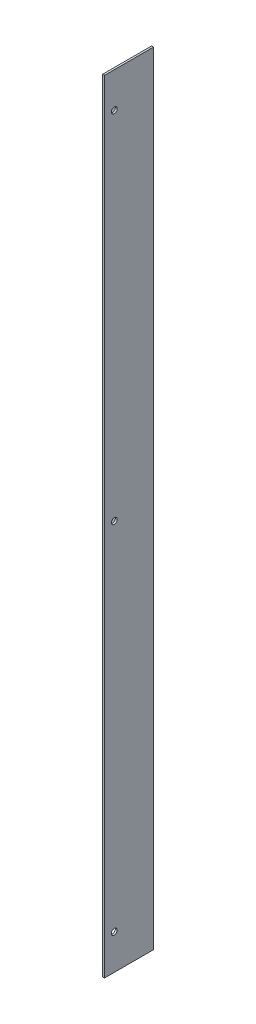
SolidWorks part; units mm, degrees
material "Plástico personalizado"
ref_plane "Alzado" through (0, 0, 0) normal (0, 0, 1) x (1, 0, 0)
ref_plane "Planta" through (0, 0, 0) normal (0, 1, 0) x (1, 0, 0)
ref_plane "Vista lateral" through (0, 0, 0) normal (1, 0, 0) x (0, 0, -1)
sketch "Croquis1" plane through (0, 0, 0) normal (0, 0, 1) x (1, 0, 0)
  line L0 (-79.4418, 83.1804) -> (-79.4418, -268.8196)
  line L2 (-55.4418, 107.1804) -> (-79.4418, 83.1804)
  line L4 (-55.4418, 107.1804) -> (-55.4418, -292.8196)
  line L5 (-55.4418, -292.8196) -> (-79.4418, -268.8196)
  circle A0 centre (-74.4418, 47.1804) radius 1.5
  circle A1 centre (-74.4418, -232.8196) radius 1.5
  dimension "D1" = 5
  dimension "D4" = 5
  dimension "D2" = 400
  dimension "D3" = 24
  dimension "D5" = 60
  dimension "D6" = 60
  dimension "D7" = 45
  dimension "D8" = 45
sketch "Croquis2" plane through (0, 0, 0) normal (0, 0, 1) x (1, 0, 0)
  line L1 (-55.4418, 107.1804) -> (-54.4418, 107.1804)
  line L2 (-55.4418, 107.1804) -> (-55.4418, -292.8196)
  line L3 (-55.4418, -292.8196) -> (-54.4418, -292.8196)
  line L4 (-54.4418, 107.1804) -> (-54.4418, -292.8196)
  dimension "D1" = 1
  dimension "D2" = 400
extrude "Saliente-Extruir2" add sketch "Croquis2" along normal blind 25
sketch "Croquis5" plane through (-54.4418, 0, 0) normal (1, 0, 0) x (0, 0, -1)
  line L0 (-25, 107.1804) -> (0, 107.1804) construction
  line L1 (-25, -292.8196) -> (0, -292.8196) construction
  line L2 (-25, -292.8196) -> (-25, 107.1804) construction
  circle A0 centre (-20, 89.1804) radius 1.5
  circle A1 centre (-20, -274.8196) radius 1.5
  circle A2 centre (-20, -92.8196) radius 1.5
  dimension "D1" = 18
  dimension "D4" = 5
  dimension "D5" = 5
  dimension "D2" = 18
  dimension "D3" = 5
  dimension "D6" = 200
extrude "Cortar-Extruir2" cut sketch "Croquis5" against normal blind 1
extrude "Saliente-Extruir3" add sketch "Croquis1" along normal blind 1
